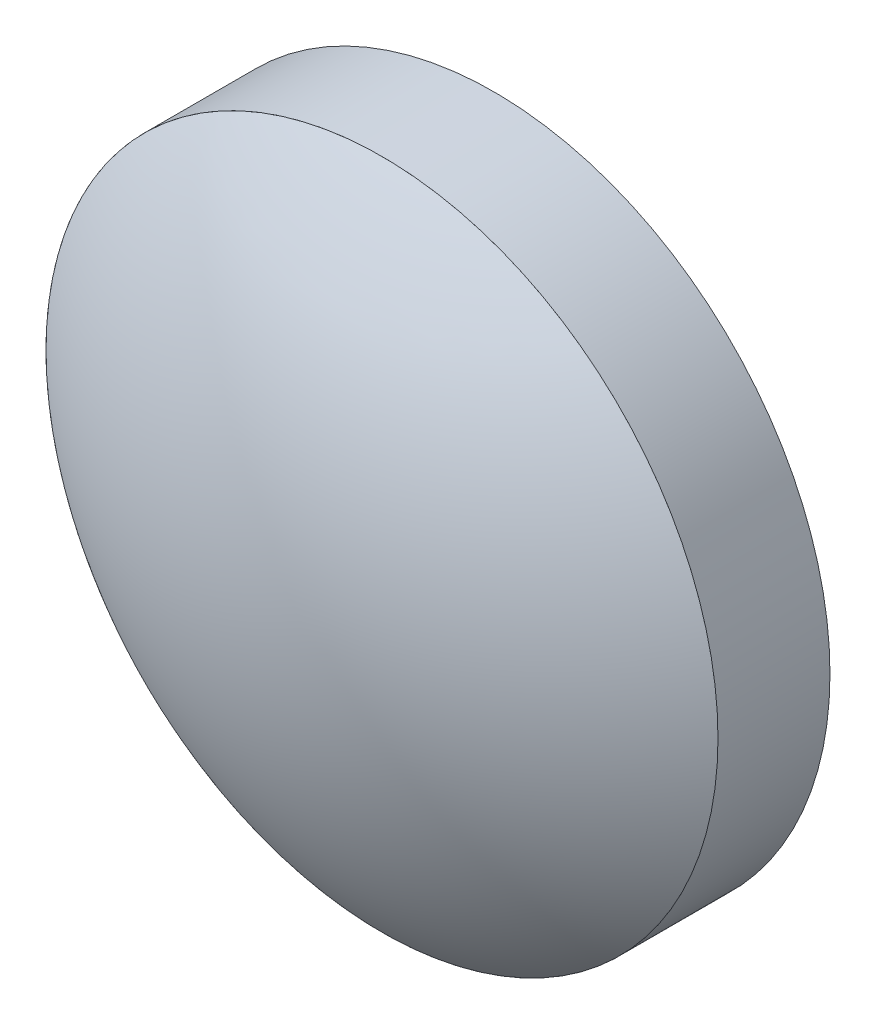
SolidWorks part; units mm, degrees
ref_plane "Front Plane" through (0, 0, 0) normal (0, 0, 1) x (1, 0, 0)
ref_plane "Top Plane" through (0, 0, 0) normal (0, 1, 0) x (1, 0, 0)
ref_plane "Right Plane" through (0, 0, 0) normal (1, 0, 0) x (0, 0, -1)
sketch "Sketch1" plane through (0, 0, 0) normal (0, 0, 1) x (1, 0, 0)
  circle A0 centre (0, 0) radius 6
  dimension "D1" = 12
extrude "Boss-Extrude1" add sketch "Sketch1" along normal blind 2
sketch "Sketch2" plane through (0, 0, 0) normal (0, 1, 0) x (1, 0, 0)
  line L0 (0, 0) -> (0, 3.8694) construction
  line L1 (6, 0) -> (-6, 0) construction
  line L3 (-6, -2) -> (-5.4854, -2)
  line L4 (-6, -2) -> (6, -2) construction
  line L5 (0, -4) -> (0, -3.7)
  arc A0 (-6, -2) -> (0, -4) centre (0, 6) ccw
  arc A1 (-5.4854, -2) -> (0, -3.7) centre (0, 6) ccw
  arc A2 (-5.82, -1.76) -> (0, -3.7) centre (0, 6) ccw construction
  arc A3 (-6, -2) -> (0, -4) centre (0, 6) ccw construction
  dimension "D2" = 2
  dimension "D1" = 0.3
revolve "Revolve1" add sketch "Sketch2" angle 360 about L0
sketch "Sketch3" plane through (0, 0, 0) normal (0, 1, 0) x (1, 0, 0)
  line L0 (0, 0) -> (0, 2.6849) construction
  line L1 (-6, -2) -> (6, -2) construction
  line L2 (-1.6, -2) -> (-1.3, -2)
  line L3 (0, -3.3) -> (0, -3.6)
  arc A0 (-1.6, -2) -> (0, -3.6) centre (0, -2) ccw
  arc A1 (-1.3, -2) -> (0, -3.3) centre (0, -2) ccw
  dimension "D1" = 1.6
  dimension "D2" = 0.3
revolve "Revolve2" add sketch "Sketch3" angle 360 about L0
sketch "Sketch4" plane through (0, 0, 2) normal (0, 0, 1) x (1, 0, 0)
  circle A0 centre (0, 0) radius 0.75
  dimension "D1" = 1.5
extrude "Cut-Extrude1" cut sketch "Sketch4" against normal blind 0.2
